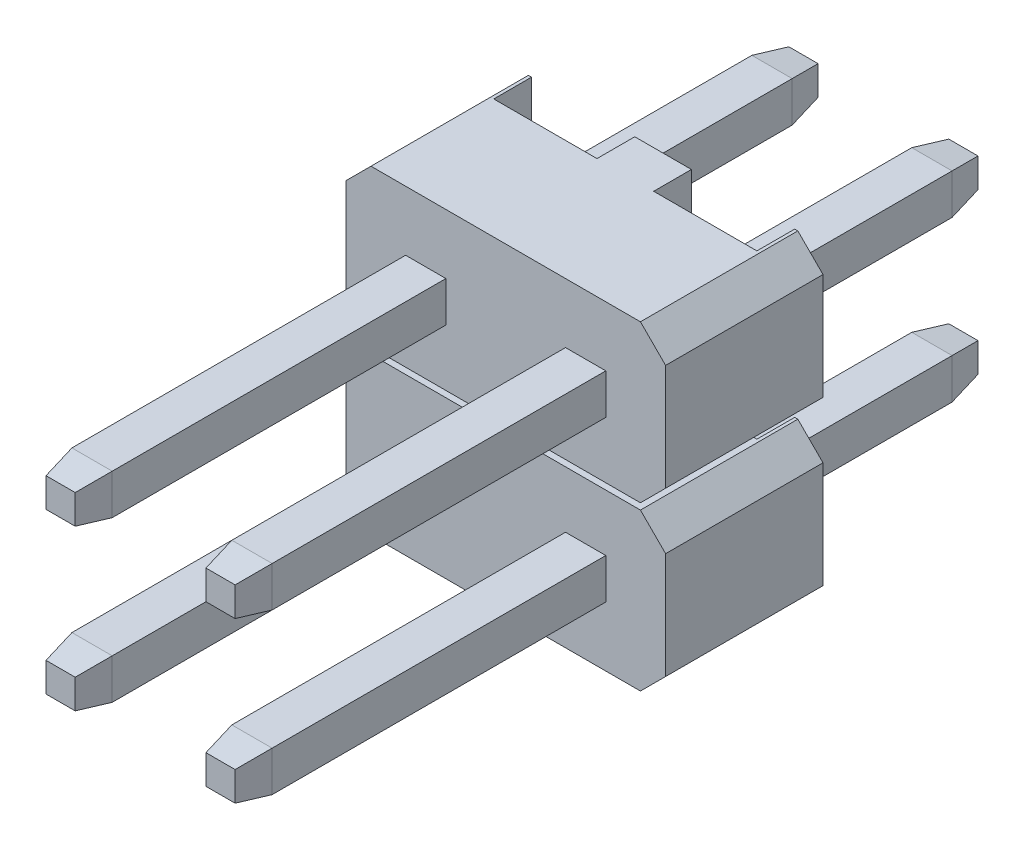
SolidWorks part; units mm, degrees
ref_plane "Płaszczyzna przednia" through (0, 0, 0) normal (0, 0, 1) x (1, 0, 0)
ref_plane "Płaszczyzna górna" through (0, 0, 0) normal (0, 1, 0) x (1, 0, 0)
ref_plane "Płaszczyzna prawa" through (0, 0, 0) normal (1, 0, 0) x (0, 0, -1)
sketch "Sketch1" plane through (0, 0, 0) normal (0, 0, 1) x (1, 0, 0)
  line L1 (1.27, 1.27) -> (-1.27, 1.27) construction
  line L2 (1.27, 1.27) -> (1.27, -1.27) construction
  line L3 (1.27, -1.27) -> (-1.27, -1.27) construction
  line L4 (-1.27, 1.27) -> (-1.27, -1.27) construction
  line L5 (1.27, 1.27) -> (-1.27, -1.27) construction
  line L6 (1.27, -1.27) -> (-1.27, 1.27) construction
  line L7 (-0.95, 0.95) -> (-1.59, 0.95)
  line L8 (-0.95, 0.95) -> (-0.95, 1.59)
  line L9 (-0.95, 1.59) -> (-1.59, 1.59)
  line L10 (-1.59, 0.95) -> (-1.59, 1.59)
  line L11 (-0.95, 0.95) -> (-1.59, 1.59) construction
  line L12 (-0.95, 1.59) -> (-1.59, 0.95) construction
  line L13 (-0.95, -0.95) -> (-1.59, -0.95)
  line L14 (-0.95, -0.95) -> (-0.95, -1.59)
  line L15 (-0.95, -1.59) -> (-1.59, -1.59)
  line L16 (-1.59, -0.95) -> (-1.59, -1.59)
  line L17 (-0.95, -0.95) -> (-1.59, -1.59) construction
  line L18 (-0.95, -1.59) -> (-1.59, -0.95) construction
  line L19 (0.95, 0.95) -> (1.59, 0.95)
  line L20 (0.95, 0.95) -> (0.95, 1.59)
  line L21 (0.95, 1.59) -> (1.59, 1.59)
  line L22 (1.59, 0.95) -> (1.59, 1.59)
  line L23 (0.95, 0.95) -> (1.59, 1.59) construction
  line L24 (0.95, 1.59) -> (1.59, 0.95) construction
  line L25 (0.95, -1.59) -> (1.59, -1.59)
  line L26 (0.95, -1.59) -> (0.95, -0.95)
  line L27 (0.95, -0.95) -> (1.59, -0.95)
  line L28 (1.59, -1.59) -> (1.59, -0.95)
  line L29 (0.95, -1.59) -> (1.59, -0.95) construction
  line L30 (0.95, -0.95) -> (1.59, -1.59) construction
  point P0 (0, 0)
extrude "Boss-Extrude1" add sketch "Sketch1" along normal blind 5.3
sketch "Sketch2" plane through (0, 0, 5.3) normal (0, 0, 1) x (1, 0, 0)
  line L4 (-1.59, -0.95) -> (-1.59, -1.59)
  line L5 (-1.59, -1.59) -> (-0.95, -1.59)
  line L6 (-0.95, -1.59) -> (-0.95, -0.95)
  line L7 (-0.95, -0.95) -> (-1.59, -0.95)
  line L8 (-1.59, -0.95) -> (-1.59, -1.59)
  line L9 (-1.59, -1.59) -> (-0.95, -1.59)
  line L10 (-0.95, -1.59) -> (-0.95, -0.95)
  line L11 (-0.95, -0.95) -> (-1.59, -0.95)
  line L12 (-1.59, 1.59) -> (-1.59, 0.95)
  line L13 (-1.59, 0.95) -> (-0.95, 0.95)
  line L14 (-0.95, 0.95) -> (-0.95, 1.59)
  line L15 (-0.95, 1.59) -> (-1.59, 1.59)
  line L16 (-1.59, 1.59) -> (-1.59, 0.95)
  line L17 (-1.59, 0.95) -> (-0.95, 0.95)
  line L18 (-0.95, 0.95) -> (-0.95, 1.59)
  line L19 (-0.95, 1.59) -> (-1.59, 1.59)
  line L20 (1.59, -1.59) -> (1.59, -0.95)
  line L21 (1.59, -0.95) -> (0.95, -0.95)
  line L22 (0.95, -0.95) -> (0.95, -1.59)
  line L23 (0.95, -1.59) -> (1.59, -1.59)
  line L24 (1.59, -1.59) -> (1.59, -0.95)
  line L25 (1.59, -0.95) -> (0.95, -0.95)
  line L26 (0.95, -0.95) -> (0.95, -1.59)
  line L27 (0.95, -1.59) -> (1.59, -1.59)
  line L28 (1.59, 0.95) -> (1.59, 1.59)
  line L29 (1.59, 1.59) -> (0.95, 1.59)
  line L30 (0.95, 1.59) -> (0.95, 0.95)
  line L31 (0.95, 0.95) -> (1.59, 0.95)
  line L32 (1.59, 0.95) -> (1.59, 1.59)
  line L33 (1.59, 1.59) -> (0.95, 1.59)
  line L34 (0.95, 1.59) -> (0.95, 0.95)
  line L35 (0.95, 0.95) -> (1.59, 0.95)
  dimension "D1" = 0
  dimension "D2" = 0
  dimension "D3" = 0
  dimension "D4" = 0
extrude "Boss-Extrude2" add sketch "Sketch2" along normal blind 0.5 draft 10
sketch "Sketch3" plane through (0, 0, 0) normal (0, 0, 1) x (1, 0, 0)
  line L1 (-2.14, 2.54) -> (2.14, 2.54)
  line L2 (-2.54, 2.14) -> (-2.54, -2.14)
  line L3 (-2.14, -2.54) -> (2.14, -2.54)
  line L4 (2.54, 2.14) -> (2.54, -2.14)
  line L5 (-2.54, 2.54) -> (2.54, -2.54) construction
  line L6 (-2.54, -2.54) -> (2.54, 2.54) construction
  line L24 (-2.54, -2.14) -> (-2.14, -2.54)
  line L25 (2.14, -2.54) -> (2.54, -2.14)
  line L26 (2.14, 2.54) -> (2.54, 2.14)
  line L27 (-2.54, 2.14) -> (-2.14, 2.54)
  point P0 (0, 0)
extrude "Boss-Extrude3" add sketch "Sketch3" against normal blind 2.5 separate body
sketch "Sketch5" plane through (0, 0, -2.5) normal (0, 0, -1) x (-1, 0, 0)
  line L0 (-0.45, -2.54) -> (-0.45, 2.54)
  line L1 (2.14, -2.54) -> (-2.14, -2.54) construction
  line L2 (-2.14, 2.54) -> (2.14, 2.54) construction
  line L3 (-2.09, -2.54) -> (-2.09, 2.54)
  line L4 (-2.54, -2.14) -> (-2.54, 2.14) construction
  line L5 (-0.95, -0.95) -> (-0.95, -1.59) construction
  line L7 (0, -2.54) -> (0, -3.101) construction
  line L8 (2.09, -2.54) -> (2.09, 2.54)
  line L9 (0.45, -2.54) -> (0.45, 2.54)
  line L10 (2.09, -2.54) -> (0.45, -2.54)
  line L11 (-0.45, -2.54) -> (-2.09, -2.54)
  line L12 (2.09, 2.54) -> (0.45, 2.54)
  line L13 (-0.45, 2.54) -> (-2.09, 2.54)
  dimension "D1" = 0.45
  dimension "D2" = 0.5
extrude "Cut-Extrude1" cut sketch "Sketch5" against normal blind 0.6
sketch "Sketch6" plane through (0, 0, 0) normal (0, 0, 1) x (1, 0, 0)
  line L0 (2.54, 0) -> (-2.54, 0) construction
  line L1 (2.54, -2.14) -> (2.54, 2.14) construction
  line L2 (-2.54, 2.14) -> (-2.54, -2.14) construction
  line L3 (-2.54, 0.05) -> (-2.54, -0.05)
  line L4 (-2.54, 0.05) -> (2.54, 0.05)
  line L5 (2.54, 0.05) -> (2.54, -0.05)
  line L6 (2.54, -0.05) -> (-2.54, -0.05)
  dimension "D1" = 0.1
extrude "Cut-Extrude2" cut sketch "Sketch6" against normal through all
sketch "Sketch7" plane through (0, 0, 0) normal (0, 0, 1) x (1, 0, 0)
  line L0 (2.54, 0.45) -> (2.14, 0.05)
  line L1 (2.54, 0.05) -> (2.54, 2.14) construction
  line L2 (2.54, 0.05) -> (-2.54, 0.05) construction
  line L3 (2.14, 0.05) -> (2.54, 0.05)
  line L4 (2.54, 0.05) -> (2.54, 0.45)
  line L5 (2.54, -0.05) -> (2.14, -0.05)
  line L6 (-2.54, -0.05) -> (2.54, -0.05) construction
  line L7 (2.14, -0.05) -> (2.54, -0.45)
  line L8 (2.54, -2.14) -> (2.54, -0.05) construction
  line L9 (2.54, -0.45) -> (2.54, -0.05)
  line L10 (0, -0.05) -> (0, 3.4542) construction
  line L11 (-2.54, -0.45) -> (-2.54, -0.05)
  line L12 (-2.14, -0.05) -> (-2.54, -0.45)
  line L13 (-2.54, -0.05) -> (-2.14, -0.05)
  line L14 (-2.54, 0.05) -> (-2.54, 0.45)
  line L15 (-2.14, 0.05) -> (-2.54, 0.05)
  line L16 (-2.54, 0.45) -> (-2.14, 0.05)
  dimension "D1" = 0.4
  dimension "D2" = 0.4
  dimension "D3" = 0.4
extrude "Cut-Extrude3" cut sketch "Sketch7" against normal through all
sketch "Sketch8" plane through (0, 0, -1.9) normal (0, 0, -1) x (-1, 0, 0)
  line L0 (1.59, -1.59) -> (0.95, -1.59)
  line L1 (0.95, -1.59) -> (0.95, -0.95)
  line L2 (0.95, -0.95) -> (1.59, -0.95)
  line L3 (1.59, -0.95) -> (1.59, -1.59)
  line L12 (0.95, 1.59) -> (1.59, 1.59) construction
  line L13 (0.95, 0.95) -> (0.95, 1.59) construction
  line L14 (1.59, 1.59) -> (1.59, 0.95) construction
  line L15 (1.59, 0.95) -> (0.95, 0.95) construction
  line L16 (-0.95, 0.95) -> (-1.59, 0.95) construction
  line L17 (-0.95, 1.59) -> (-0.95, 0.95) construction
  line L18 (-1.59, 1.59) -> (-0.95, 1.59) construction
  line L19 (-1.59, 0.95) -> (-1.59, 1.59) construction
  line L20 (-1.59, -0.95) -> (-0.95, -0.95) construction
  line L21 (-1.59, -1.59) -> (-1.59, -0.95) construction
  line L22 (-0.95, -0.95) -> (-0.95, -1.59) construction
  line L23 (-0.95, -1.59) -> (-1.59, -1.59) construction
  line L32 (0.95, 1.59) -> (1.59, 1.59)
  line L33 (0.95, 0.95) -> (0.95, 1.59)
  line L34 (1.59, 1.59) -> (1.59, 0.95)
  line L35 (1.59, 0.95) -> (0.95, 0.95)
  line L36 (-0.95, 0.95) -> (-1.59, 0.95)
  line L37 (-0.95, 1.59) -> (-0.95, 0.95)
  line L38 (-1.59, 1.59) -> (-0.95, 1.59)
  line L39 (-1.59, 0.95) -> (-1.59, 1.59)
  line L40 (-1.59, -0.95) -> (-0.95, -0.95)
  line L41 (-1.59, -1.59) -> (-1.59, -0.95)
  line L42 (-0.95, -0.95) -> (-0.95, -1.59)
  line L43 (-0.95, -1.59) -> (-1.59, -1.59)
extrude "Boss-Extrude4" add sketch "Sketch8" along normal blind 3.6 separate body
sketch "Sketch9" plane through (0, 0, -5.5) normal (0, 0, -1) x (-1, 0, 0)
  line L4 (0.95, 1.59) -> (0.95, 0.95)
  line L5 (0.95, 0.95) -> (1.59, 0.95)
  line L6 (1.59, 0.95) -> (1.59, 1.59)
  line L7 (1.59, 1.59) -> (0.95, 1.59)
  line L8 (0.95, 1.59) -> (0.95, 0.95)
  line L9 (0.95, 0.95) -> (1.59, 0.95)
  line L10 (1.59, 0.95) -> (1.59, 1.59)
  line L11 (1.59, 1.59) -> (0.95, 1.59)
  line L12 (1.59, -1.59) -> (1.59, -0.95)
  line L13 (1.59, -0.95) -> (0.95, -0.95)
  line L14 (0.95, -0.95) -> (0.95, -1.59)
  line L15 (0.95, -1.59) -> (1.59, -1.59)
  line L16 (1.59, -1.59) -> (1.59, -0.95)
  line L17 (1.59, -0.95) -> (0.95, -0.95)
  line L18 (0.95, -0.95) -> (0.95, -1.59)
  line L19 (0.95, -1.59) -> (1.59, -1.59)
  line L20 (-1.59, -0.95) -> (-1.59, -1.59)
  line L21 (-1.59, -1.59) -> (-0.95, -1.59)
  line L22 (-0.95, -1.59) -> (-0.95, -0.95)
  line L23 (-0.95, -0.95) -> (-1.59, -0.95)
  line L24 (-1.59, -0.95) -> (-1.59, -1.59)
  line L25 (-1.59, -1.59) -> (-0.95, -1.59)
  line L26 (-0.95, -1.59) -> (-0.95, -0.95)
  line L27 (-0.95, -0.95) -> (-1.59, -0.95)
  line L28 (-0.95, 0.95) -> (-0.95, 1.59)
  line L29 (-0.95, 1.59) -> (-1.59, 1.59)
  line L30 (-1.59, 1.59) -> (-1.59, 0.95)
  line L31 (-1.59, 0.95) -> (-0.95, 0.95)
  line L32 (-0.95, 0.95) -> (-0.95, 1.59)
  line L33 (-0.95, 1.59) -> (-1.59, 1.59)
  line L34 (-1.59, 1.59) -> (-1.59, 0.95)
  line L35 (-1.59, 0.95) -> (-0.95, 0.95)
  dimension "D1" = 0
  dimension "D2" = 0
  dimension "D3" = 0
  dimension "D4" = 0
extrude "Boss-Extrude5" add sketch "Sketch9" along normal blind 0.5 draft 10
